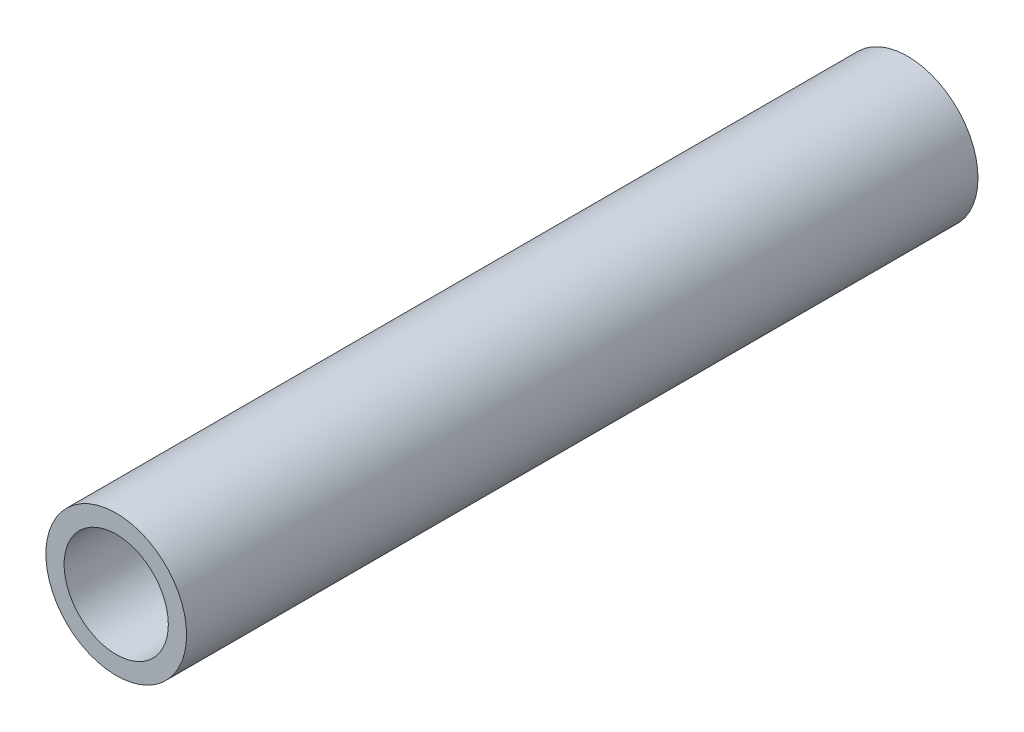
SolidWorks part; units mm, degrees
ref_plane "Front Plane" through (0, 0, 0) normal (0, 0, 1) x (1, 0, 0)
ref_plane "Top Plane" through (0, 0, 0) normal (0, 1, 0) x (1, 0, 0)
ref_plane "Right Plane" through (0, 0, 0) normal (1, 0, 0) x (0, 0, -1)
sketch "Sketch1" plane through (0, 0, 0) normal (0, 0, 1) x (1, 0, 0)
  circle A0 centre (0, 0) radius 10.668
  dimension "Pipe OD" = 21.336
extrude "Extrude-Thin1" add sketch "Sketch1" along normal mid plane 120 thin thin type one direction reverse wall 2.7686
